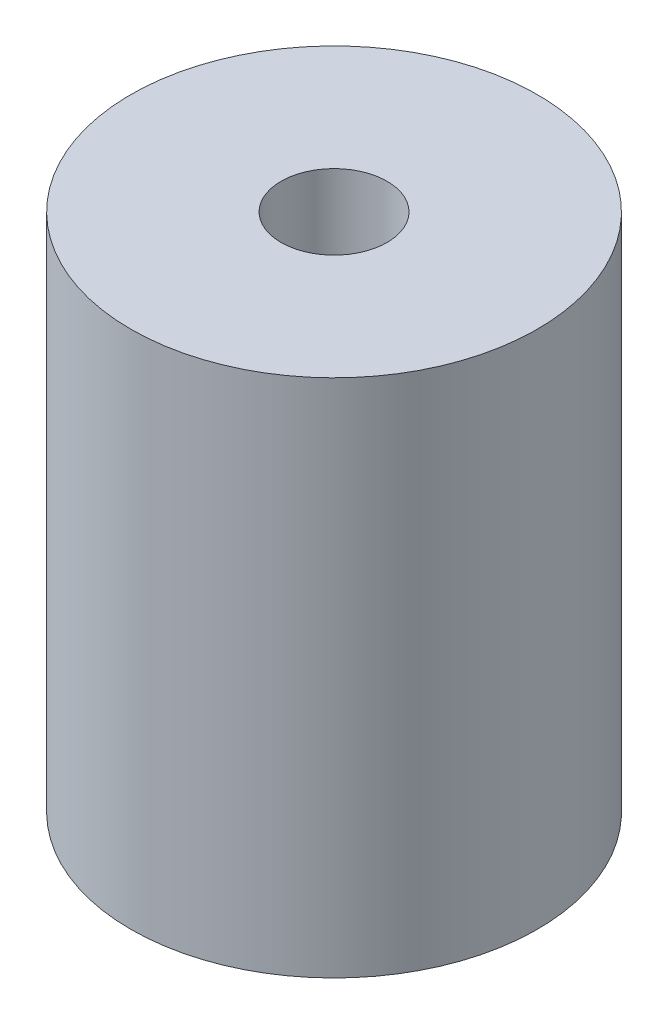
SolidWorks part; units mm, degrees
ref_plane "Front Plane" through (0, 0, 0) normal (0, 0, 1) x (1, 0, 0)
ref_plane "Top Plane" through (0, 0, 0) normal (0, 1, 0) x (1, 0, 0)
ref_plane "Right Plane" through (0, 0, 0) normal (1, 0, 0) x (0, 0, -1)
sketch "Sketch1" plane through (0, 0, 0) normal (0, 1, 0) x (1, 0, 0)
  circle A0 centre (0, 0) radius 9.58
  circle A1 centre (0, 0) radius 4
  dimension "D1" = 8
  dimension "D2" = 19.16
extrude "Boss-Extrude1" add sketch "Sketch1" along normal blind 18
sketch "Sketch2" plane through (0, 18, 0) normal (0, 1, 0) x (1, 0, 0)
  circle A0 centre (0, 0) radius 2.5
  circle A1 centre (0, 0) radius 9.58
  dimension "D1" = 19.16
  dimension "D2" = 5
extrude "Boss-Extrude2" add sketch "Sketch2" along normal blind 6.5
